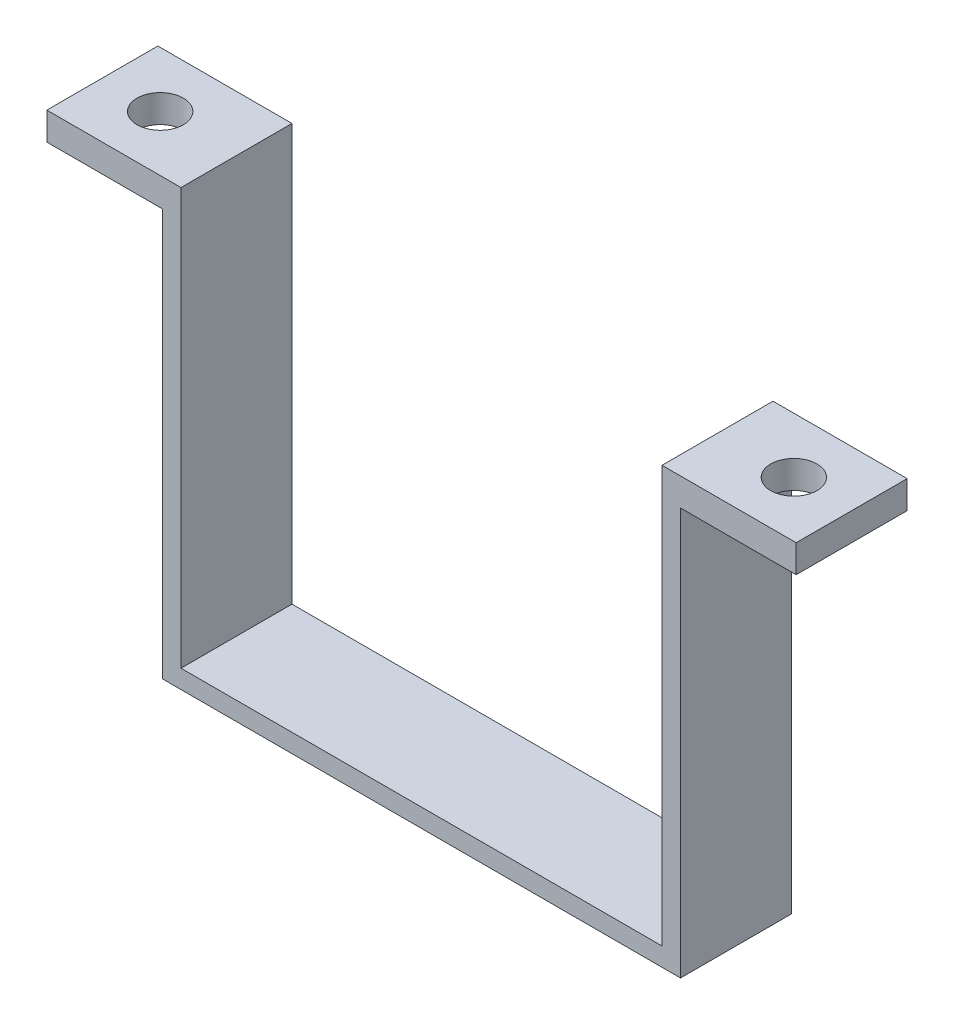
SolidWorks part; units mm, degrees
material "ABS PC"
ref_plane "Front Plane" through (0, 0, 0) normal (0, 0, 1) x (1, 0, 0)
ref_plane "Top Plane" through (0, 0, 0) normal (0, 1, 0) x (1, 0, 0)
ref_plane "Right Plane" through (0, 0, 0) normal (1, 0, 0) x (0, 0, -1)
sketch "Sketch1" plane through (0, 0, 0) normal (0, 0, 1) x (1, 0, 0)
  line L0 (0, 0) -> (0, 3)
  line L1 (0, 3) -> (12, 3)
  line L2 (12, 3) -> (12, 0)
  line L3 (12, 0) -> (2, 0)
  line L4 (0, 0) -> (0, -42)
  line L5 (2, 0) -> (2, -44)
  line L6 (0, -42) -> (-52, -42)
  line L7 (2, -44) -> (-54, -44)
  line L8 (-52, -42) -> (-52, 3)
  line L9 (-52, 3) -> (-64, 3)
  line L10 (-54, -44) -> (-54, 0)
  line L11 (-64, 3) -> (-64, 0)
  line L12 (-64, 0) -> (-54, 0)
  dimension "D1" = 12
  dimension "D2" = 3
  dimension "D3" = 10
  dimension "D4" = 3
  dimension "D5" = 42
  dimension "D6" = 44
  dimension "D7" = 52
  dimension "D8" = 56
  dimension "D9" = 12
  dimension "D10" = 45
extrude "Boss-Extrude1" add sketch "Sketch1" along normal blind 12
sketch "Sketch3" plane through (12, 0, 0) normal (1, 0, 0) x (0, 0, -1)
  line L1 (-12, 0) -> (0, 0)
  line L2 (-12, 0) -> (-12, 3)
  line L3 (-12, 3) -> (0, 3)
  line L4 (0, 0) -> (0, 3)
extrude "Boss-Extrude2" add sketch "Sketch3" along normal blind 2.5
sketch "Sketch4" plane through (-64, 0, 0) normal (-1, 0, 0) x (0, 0, 1)
  line L1 (0, 0) -> (12, 0)
  line L2 (0, 0) -> (0, 3)
  line L3 (0, 3) -> (12, 3)
  line L4 (12, 0) -> (12, 3)
extrude "Boss-Extrude3" add sketch "Sketch4" along normal blind 2.5
sketch "Sketch6" plane through (0, 0, 0) normal (0, -1, 0) x (1, 0, 0)
  line L0 (-66.5, 6) -> (-60.25, 6)
  line L1 (-66.5, 0) -> (-66.5, 12) construction
  circle A0 centre (-60.25, 6) radius 2.5
  dimension "D2" = 5
  dimension "D1" = 6.25
extrude "Cut-Extrude1" cut sketch "Sketch6" against normal blind 10
sketch "Sketch7" plane through (0, 0, 0) normal (0, -1, 0) x (1, 0, 0)
  line L0 (14.5, 6) -> (8.25, 6)
  line L1 (14.5, 12) -> (14.5, 0) construction
  circle A0 centre (8.25, 6) radius 2.5
  dimension "D2" = 5
  dimension "D1" = 6.25
extrude "Cut-Extrude2" cut sketch "Sketch7" against normal blind 10
